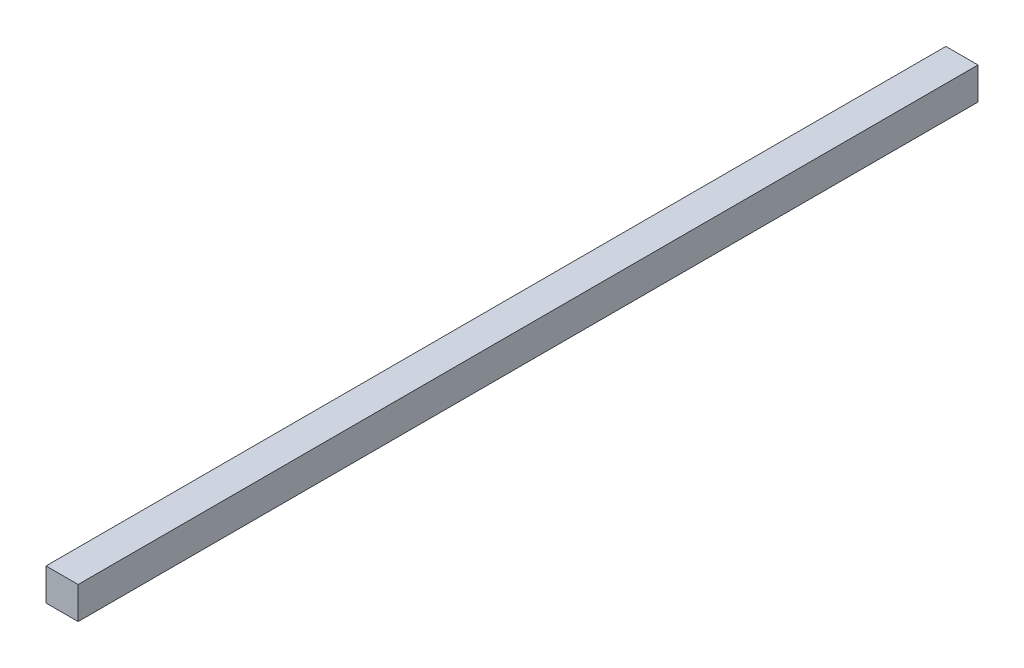
SolidWorks part; units mm, degrees
ref_plane "Plan de face" through (0, 0, 0) normal (0, 0, 1) x (1, 0, 0)
ref_plane "Plan de dessus" through (0, 0, 0) normal (0, 1, 0) x (1, 0, 0)
ref_plane "Plan de droite" through (0, 0, 0) normal (1, 0, 0) x (0, 0, -1)
sketch "Esquisse1" plane through (0, 0, 0) normal (0, 0, 1) x (1, 0, 0)
  line L1 (-7.5, -7.5) -> (7.5, -7.5)
  line L2 (-7.5, -7.5) -> (-7.5, 7.5)
  line L3 (-7.5, 7.5) -> (7.5, 7.5)
  line L4 (7.5, -7.5) -> (7.5, 7.5)
  line L5 (-7.5, -7.5) -> (7.5, 7.5) construction
  line L6 (-7.5, 7.5) -> (7.5, -7.5) construction
  point P0 (0, 0)
  dimension "D1" = 15
  dimension "D2" = 15
extrude "Boss.-Extru.1" add sketch "Esquisse1" along normal blind 420
